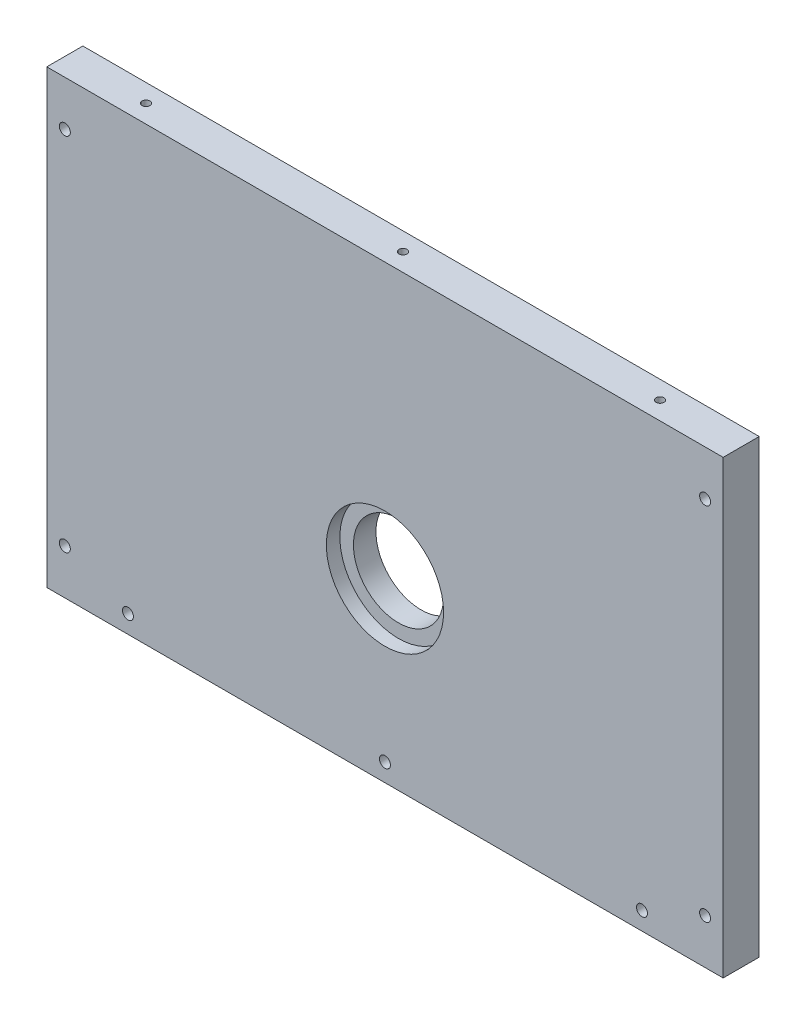
SolidWorks part; units mm, degrees
ref_plane "Front Plane" through (0, 0, 0) normal (0, 0, 1) x (1, 0, 0)
ref_plane "Top Plane" through (0, 0, 0) normal (0, 1, 0) x (1, 0, 0)
ref_plane "Right Plane" through (0, 0, 0) normal (1, 0, 0) x (0, 0, -1)
sketch "Sketch1" plane through (0, 0, 0) normal (0, 0, 1) x (1, 0, 0)
  line L1 (0, 0) -> (150, 0)
  line L2 (0, 0) -> (0, 100)
  line L3 (0, 100) -> (150, 100)
  line L4 (150, 0) -> (150, 100)
  dimension "D1" = 100
  dimension "D2" = 150
extrude "Boss-Extrude1" add sketch "Sketch1" along normal blind 8
hole_wizard "CBORE for #2 Socket Head Cap Screw1" positions "Sketch3" profile "Sketch2" counterbore size "#2" standard "ANSI Inch" end condition through all
sketch "Sketch3" plane through (0, 0, 0) normal (0, 0, -1) x (-1, 0, 0)
  line L0 (-150, 100) -> (0, 100) construction
  line L1 (-142, 100) -> (-142, 0)
  line L2 (0, 0) -> (-150, 0) construction
  line L4 (-150, 0) -> (-150, 100) construction
  line L5 (-8, 100) -> (-8, 0)
  line L7 (0, 100) -> (0, 0) construction
  point P0 (-132, 4)
  point P1 (-18, 4)
  point P3 (-4, 90)
  point P5 (-146, 90)
  point P23 (-4, 90)
  point P32 (-146, 10)
  point P34 (-4, 10)
  point P40 (-75, 4)
  point P43 (-75, 0)
  dimension "D1" = 8
  dimension "D2" = 8
  dimension "D3" = 10
  dimension "D4" = 4
  dimension "D5" = 10
  dimension "D6" = 4
  dimension "D7" = 4
  dimension "D8" = 10
  dimension "D9" = 4
  dimension "D10" = 10
  dimension "D11" = 4
  dimension "D12" = 10
  dimension "D13" = 10
  dimension "D14" = 4
  dimension "D15" = 4
  dimension "D16" = 4
sketch "Sketch2" plane through (132, 4, 0) normal (1, 0, 0) x (0, 1, 0)
  line L0 (0, 0) -> (0, 8)
  line L1 (0, 8) -> (1.2192, 8)
  line L3 (1.2192, 8) -> (1.2192, 2.1844)
  line L4 (1.2192, 2.1844) -> (2.3812, 2.1844)
  line L5 (2.3812, 2.1844) -> (2.3812, 0)
  line L7 (2.3812, 0) -> (0, 0)
  line L11 (0, -6.35) -> (0, 107.95) construction
  dimension "Thru Hole Dia." = 2.4384
  dimension "Thru Hole Depth" = 8
  dimension "C'Bore Dia." = 4.7625
  dimension "C'Bore Depth" = 2.1844
sketch "Sketch4" plane through (0, 0, 8) normal (0, 0, 1) x (1, 0, 0)
  line L0 (0, 9.9) -> (150, 9.9)
  line L1 (0, 100) -> (0, 0) construction
  line L2 (150, 0) -> (150, 100) construction
  line L3 (0, 0) -> (150, 0) construction
  line L4 (130, 100) -> (130, 0)
  line L5 (150, 100) -> (0, 100) construction
  line L6 (85, 100) -> (85, 0)
  dimension "D1" = 9.9
  dimension "D2" = 20
  dimension "D3" = 45
sketch "Sketch5" plane through (0, 0, 8) normal (0, 0, 1) x (1, 0, 0)
  line L1 (0, 9.9) -> (150, 9.9) construction
  line L2 (150, 100) -> (0, 100) construction
  circle A0 centre (75, 39.2) radius 10
  point P6 (75, 100)
  dimension "D1" = 0
  dimension "D2" = 29.3
extrude "Cut-Extrude1" cut sketch "Sketch5" against normal through all
sketch "Sketch6" plane through (0, 0, 8) normal (0, 0, 1) x (1, 0, 0)
  line L1 (0, 9.9) -> (150, 9.9) construction
  line L2 (150, 100) -> (0, 100) construction
  circle A0 centre (75, 39.2) radius 13
  point P6 (75, 100)
  dimension "D1" = 0
  dimension "D2" = 29.3
extrude "Cut-Extrude2" cut sketch "Sketch6" against normal blind 3
hole_wizard "#2-56 Tapped Hole1" positions "Sketch7" profile "Sketch8" tap size "#2-56" standard "ANSI Inch"
sketch "Sketch7" plane through (0, 100, 0) normal (0, 1, 0) x (1, 0, 0)
  line L0 (8, 0) -> (8, -8)
  line L1 (150, 0) -> (0, 0) construction
  line L2 (0, -8) -> (150, -8) construction
  line L4 (0, -8) -> (0, 0) construction
  line L5 (142, 0) -> (142, -8)
  line L7 (150, -8) -> (150, 0) construction
  point P0 (18, -4)
  point P2 (75, -4)
  point P4 (132, -4)
  point P24 (75, -8)
  dimension "D1" = 8
  dimension "D2" = 8
  dimension "D3" = 10
  dimension "D4" = 4
  dimension "D5" = 4
  dimension "D6" = 10
  dimension "D7" = 4
  dimension "D8" = 0
sketch "Sketch8" plane through (18, 100, 4) normal (1, 0, 0) x (0, 0, 1)
  line L0 (0, 0) -> (0, 15.5342)
  line L1 (0, 15.5342) -> (0.889, 15)
  line L2 (0.889, 15) -> (0.889, 0)
  line L5 (0.889, 0) -> (0, 0)
  line L10 (0, 15.5342) -> (-0.889, 15) construction
  line L11 (0, -6.35) -> (0, 107.95) construction
  dimension "Tap Drill Dia." = 1.778
  dimension "Tap Drill Depth" = 15
  dimension "Drill Angle" = 118
cosmetic thread "Hole Thread1" parameters "D1"=12, "D2"=2.1844
cosmetic thread "Hole Thread2" parameters "D1"=12, "D2"=2.1844
cosmetic thread "Hole Thread3" parameters "D1"=12, "D2"=2.1844
